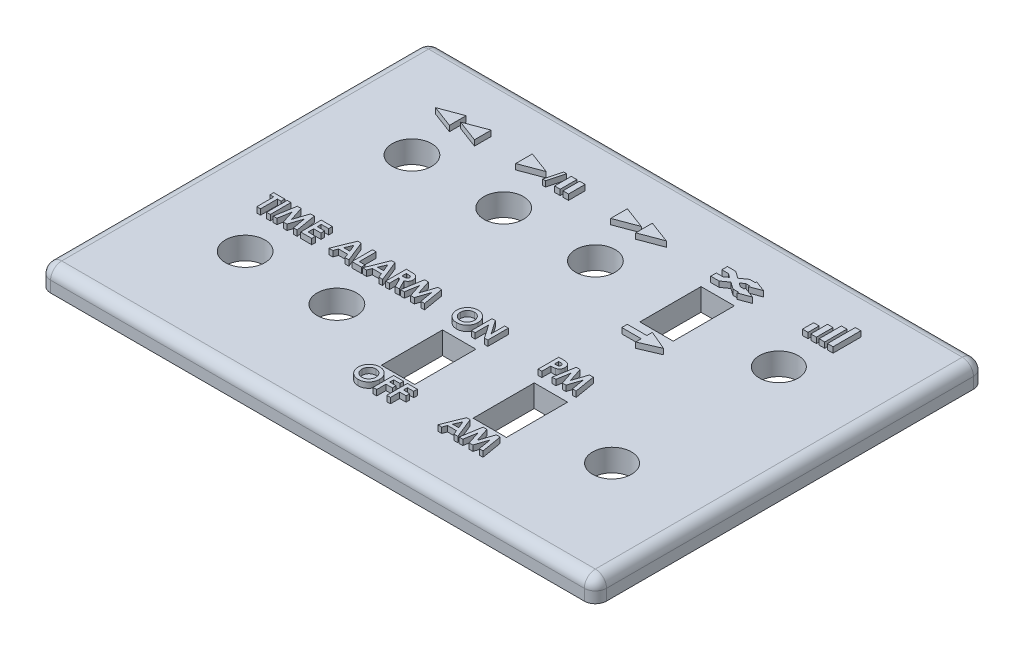
SolidWorks part; units mm, degrees
ref_plane "Front Plane" through (0, 0, 0) normal (0, 0, 1) x (1, 0, 0)
ref_plane "Top Plane" through (0, 0, 0) normal (0, 1, 0) x (1, 0, 0)
ref_plane "Right Plane" through (0, 0, 0) normal (1, 0, 0) x (0, 0, -1)
sketch "Sketch1" plane through (0, 0, 0) normal (0, 1, 0) x (1, 0, 0)
  line L0 (44.75, -15) -> (50, -15) construction
  line L1 (-50, -35) -> (50, -35)
  line L2 (-50, -35) -> (-50, 35)
  line L3 (-50, 35) -> (50, 35)
  line L4 (50, -35) -> (50, 35)
  line L5 (-50, -35) -> (50, 35) construction
  line L6 (-50, 35) -> (50, -35) construction
  circle A0 centre (33, -15) radius 11.75 construction
  point P0 (0, 0)
  dimension "D1" = 100
  dimension "D2" = 70
  dimension "D3" = 5.25
extrude "Boss-Extrude1" add sketch "Sketch1" along normal blind 4
sketch "Sketch2" plane through (0, 4, 0) normal (0, 1, 0) x (1, 0, 0)
  line L0 (-33, 15) -> (-16.5, 15) construction
  line L1 (13.5, 9.5) -> (19.5, 9.5)
  line L2 (13.5, 9.5) -> (13.5, 20.5)
  line L3 (13.5, 20.5) -> (19.5, 20.5)
  line L4 (19.5, 9.5) -> (19.5, 20.5)
  line L5 (13.5, 9.5) -> (19.5, 20.5) construction
  line L6 (13.5, 20.5) -> (19.5, 9.5) construction
  line L7 (-3, -9.5) -> (3, -9.5)
  line L8 (-3, -9.5) -> (-3, -20.5)
  line L9 (-3, -20.5) -> (3, -20.5)
  line L10 (3, -9.5) -> (3, -20.5)
  line L11 (-3, -9.5) -> (3, -20.5) construction
  line L12 (-3, -20.5) -> (3, -9.5) construction
  line L13 (13.5, -9.5) -> (19.5, -9.5)
  line L14 (13.5, -9.5) -> (13.5, -20.5)
  line L15 (13.5, -20.5) -> (19.5, -20.5)
  line L16 (19.5, -9.5) -> (19.5, -20.5)
  line L17 (13.5, -9.5) -> (19.5, -20.5) construction
  line L18 (13.5, -20.5) -> (19.5, -9.5) construction
  line L19 (-16.5, 15) -> (0, 15) construction
  line L20 (-33, -15) -> (-16.5, -15) construction
  line L21 (0, 15) -> (16.5, 15) construction
  line L22 (16.5, 15) -> (33, 15) construction
  line L23 (-16.5, -15) -> (0, -15) construction
  line L24 (0, -15) -> (16.5, -15) construction
  line L25 (16.5, -15) -> (33, -15) construction
  line L26 (-33, 15) -> (-50, 15) construction
  line L27 (-50, 35) -> (-50, -35) construction
  line L28 (33, 15) -> (50, 15) construction
  line L29 (50, -35) -> (50, 35) construction
  line L30 (-33, 15) -> (-33, 35) construction
  line L31 (50, 35) -> (-50, 35) construction
  line L32 (-33, -15) -> (-33, -35) construction
  line L33 (-50, -35) -> (50, -35) construction
  circle A0 centre (-33, -15) radius 3.55
  circle A1 centre (-16.5, -15) radius 3.55
  circle A2 centre (33, -15) radius 3.5
  circle A4 centre (-33, 15) radius 3.55
  circle A5 centre (-16.5, 15) radius 3.55
  circle A6 centre (0, 15) radius 3.55
  circle A7 centre (33, 15) radius 3.5
  point P4 (0, -15)
  point P14 (16.5, 15)
  point P21 (16.5, -15)
  dimension "D1" = 7
  dimension "D2" = 7.1
  dimension "D3" = 11
  dimension "D4" = 16.5
  dimension "D5" = 30
  dimension "D6" = 6
extrude "Cut-Extrude1" cut sketch "Sketch2" against normal through all
sketch "Sketch4" plane through (0, 4, 0) normal (0, 1, 0) x (1, 0, 0)
  line L0 (-33.25, 22) -> (-37.25, 23.5)
  line L1 (-37.25, 23.5) -> (-33.25, 25)
  line L2 (-33.25, 25) -> (-33.25, 22)
  line L3 (-37.25, 23.5) -> (-33.25, 23.5) construction
  line L4 (-28.75, 22) -> (-32.75, 23.5)
  line L5 (-32.75, 23.5) -> (-28.75, 25)
  line L6 (-28.75, 25) -> (-28.75, 22)
  line L7 (-32.75, 23.5) -> (-28.75, 23.5) construction
  line L8 (-33, 15) -> (-33, 38.4844) construction
  line L9 (-16.5, 15) -> (-16.5, 59.3156) construction
  line L10 (0, 15) -> (0, 58.3812) construction
  line L11 (-0.25, 23.5) -> (-4.25, 23.5) construction
  line L12 (4.25, 23.5) -> (0.25, 23.5) construction
  line L13 (-4.25, 25) -> (-4.25, 22)
  line L14 (-0.25, 23.5) -> (-4.25, 25)
  line L15 (-4.25, 22) -> (-0.25, 23.5)
  line L16 (0.25, 25) -> (0.25, 22)
  line L17 (4.25, 23.5) -> (0.25, 25)
  line L18 (0.25, 22) -> (4.25, 23.5)
  line L19 (-21.3393, 25) -> (-21.3393, 22)
  line L20 (-14.3393, 22) -> (-13.3393, 22)
  line L21 (-14.3393, 22) -> (-14.3393, 25)
  line L22 (-14.3393, 25) -> (-13.3393, 25)
  line L23 (-13.3393, 22) -> (-13.3393, 25)
  line L24 (-12.8393, 22) -> (-11.8393, 22)
  line L25 (-12.8393, 22) -> (-12.8393, 25)
  line L26 (-12.8393, 25) -> (-11.8393, 25)
  line L27 (-11.8393, 22) -> (-11.8393, 25)
  line L28 (-21.3393, 22) -> (-17.3393, 23.5)
  line L29 (-17.3393, 23.5) -> (-21.3393, 25)
  line L30 (-17.3393, 23.5) -> (-21.3393, 23.5) construction
  line L31 (-16.5, 22) -> (-15.6962, 25)
  line L32 (-15.6962, 25) -> (-15.1785, 25)
  line L33 (-15.1785, 25) -> (-15.9824, 22)
  line L34 (-15.9824, 22) -> (-16.5, 22)
  line L35 (-16.5, 22) -> (-15.1785, 25) construction
  line L36 (-11.2285, 22) -> (-11.8393, 22) construction
  line L37 (-15.6962, 25) -> (-15.9824, 22) construction
  line L38 (13.75, 25) -> (15.25, 25)
  line L39 (15.25, 25) -> (18.0687, 23)
  line L40 (18.0687, 23) -> (18.75, 23)
  line L41 (18.75, 23) -> (18.75, 23.25)
  line L42 (18.75, 23.25) -> (20.75, 22.5)
  line L43 (20.75, 22.5) -> (18.75, 21.75)
  line L44 (18.75, 21.75) -> (18.75, 22)
  line L45 (18.75, 22) -> (17.75, 22)
  line L46 (17.75, 22) -> (14.9313, 24)
  line L47 (14.9313, 24) -> (13.75, 24)
  line L48 (13.75, 23) -> (14.9313, 23)
  line L49 (14.9313, 23) -> (17.75, 25)
  line L50 (17.75, 25) -> (18.75, 25)
  line L51 (18.75, 25) -> (18.75, 25.25)
  line L52 (18.75, 25.25) -> (20.75, 24.5)
  line L53 (20.75, 24.5) -> (18.75, 23.75)
  line L54 (18.75, 23.75) -> (18.75, 24)
  line L55 (18.75, 24) -> (18.0687, 24)
  line L56 (18.0687, 24) -> (15.25, 22)
  line L57 (15.25, 22) -> (13.75, 22)
  line L58 (13.75, 22) -> (13.75, 23)
  line L59 (13.75, 24) -> (13.75, 25)
  line L60 (13.5, 9.5) -> (19.5, 9.5) construction
  line L61 (16.5, 9.5) -> (16.5, 48.0375) construction
  line L62 (13.75, 7) -> (17.25, 7)
  line L63 (17.25, 7) -> (17.25, 8)
  line L64 (17.25, 8) -> (20.75, 6.5)
  line L65 (20.75, 6.5) -> (17.25, 5)
  line L66 (17.25, 5) -> (17.25, 6)
  line L67 (17.25, 6) -> (13.75, 6)
  line L68 (13.75, 6) -> (13.75, 7)
  line L69 (26.3972, 23.5) -> (38.927, 23.5) construction
  line L70 (30.25, 22) -> (35.75, 22) construction
  line L71 (30.25, 22) -> (31.25, 22)
  line L72 (30.25, 22) -> (30.25, 24)
  line L73 (30.25, 24) -> (31.25, 24)
  line L74 (31.25, 22) -> (31.25, 24)
  line L75 (31.75, 22) -> (32.75, 22)
  line L76 (31.75, 22) -> (31.75, 25)
  line L77 (31.75, 25) -> (32.75, 25)
  line L78 (32.75, 22) -> (32.75, 25)
  line L79 (33.25, 22) -> (34.25, 22)
  line L80 (33.25, 22) -> (33.25, 26)
  line L81 (33.25, 26) -> (34.25, 26)
  line L82 (34.25, 22) -> (34.25, 26)
  line L83 (34.75, 22) -> (35.75, 22)
  line L84 (34.75, 22) -> (34.75, 27)
  line L85 (34.75, 27) -> (35.75, 27)
  line L86 (35.75, 22) -> (35.75, 27)
  line L87 (33, 22) -> (33, 15)
  line L92 (50, -35) -> (50, 35)
  line L93 (50, 35) -> (-50, 35)
  line L94 (-50, 35) -> (-50, -35)
  line L95 (-50, -35) -> (50, -35)
  line L96 (50, -35) -> (50, 35)
  line L97 (50, 35) -> (-50, 35)
  line L98 (-50, 35) -> (-50, -35)
  line L99 (-50, -35) -> (50, -35)
  circle A0 centre (33, 15) radius 3.5 construction
  circle A1 centre (33, 15) radius 3.5 construction
  point P35 (-15.8393, 23.5)
  point P70 (16.5, 22.8869)
  point P78 (17.364, 23.5)
  dimension "D1" = 4
  dimension "D2" = 3
  dimension "D3" = 0.5
  dimension "D4" = 0.25
  dimension "D5" = 8.5
  dimension "D6" = 3
  dimension "D7" = 4
  dimension "D8" = 0.5
  dimension "D9" = 3
  dimension "D10" = 7
  dimension "D11" = 3
  dimension "D12" = 1
  dimension "D13" = 0.5
  dimension "D14" = 1.5
  dimension "D15" = 1.5
  dimension "D16" = 75
  dimension "D17" = 1
  dimension "D18" = 1
  dimension "D19" = 1
  dimension "D20" = 1
  dimension "D21" = 1
  dimension "D22" = 1
  dimension "D23" = 1.5
  dimension "D24" = 3
  dimension "D25" = 7
  dimension "D26" = 1.5
  dimension "D27" = 2
  dimension "D28" = 3
  dimension "D29" = 8.5
  dimension "D30" = 1
  dimension "D31" = 3
  dimension "D32" = 7
  dimension "D33" = 3.5
  dimension "D34" = 8.5
  dimension "D35" = 0.5
  dimension "D36" = 1
  dimension "D37" = 0.5
  dimension "D38" = 0.5
  dimension "D39" = 1
  dimension "D40" = 1
  dimension "D41" = 1
  dimension "D43" = 5
  dimension "D42" = 0
extrude "Boss-Extrude5" add sketch "Sketch4" along normal blind 1 contours L2 L1 L0 | L6 L5 L4 | L28 L29 L19 | L34 L33 L32 L31 | L20 L23 L22 L21 | L24 L27 L26 L25 | L13 L15 L14 | L16 L18 L17 | L59 L47 L46 L49 L39 L38 | L56 L55 L54 L53 L52 L51 L50 L49 L39 | L56 L39 L49 L46 | L58 L57 L56 L46 L49 L48 | L39 L56 L46 L45 L44 L43 L42 L41 L40 | L68 L67 L66 L65 L64 L63 L62 | L71 L74 L73 L72 | L75 L78 L77 L76 | L79 L82 L81 L80 | L83 L86 L85 L84
sketch "Sketch5" plane through (0, 4, 0) normal (0, 1, 0) x (1, 0, 0)
  line L0 (-38.6119, -8) -> (-27.3881, -8) construction
  line L1 (-25.0167, -8) -> (-7.9833, -8) construction
  line L2 (-4.0464, -8) -> (4.0464, -8) construction
  line L3 (-33, -8) -> (-33, -15) construction
  line L4 (12.2763, -8) -> (20.7237, -8) construction
  line L5 (-16.5, -8) -> (-16.5, -15) construction
  line L6 (0, -8) -> (0, -15) construction
  line L7 (16.5, -8) -> (16.5, -15) construction
  line L8 (0, -15) -> (0, -25.7) construction
  line L9 (16.5, -15) -> (16.5, -25.7) construction
  line L10 (-4.0464, -25.7) -> (4.0464, -25.7) construction
  line L11 (12.2763, -25.7) -> (20.7237, -25.7) construction
  line L12 (-33, -15) -> (33, -15) construction
  line L13 (-3, -9.5) -> (3, -20.5) construction
  line L14 (-3, -20.5) -> (3, -9.5) construction
  line L15 (13.5, -9.5) -> (19.5, -20.5) construction
  line L16 (13.5, -20.5) -> (19.5, -9.5) construction
  circle A0 centre (-33, -15) radius 3.55 construction
  circle A1 centre (-33, -15) radius 3.55 construction
  text T0 "<b>TIME</b>" font "Century Gothic" height in points 14
  text T1 "<b>ALARM</b>" font "Century Gothic" height in points 14
  text T2 "<b>ON</b>" font "Century Gothic" height in points 14
  text T3 "<b>OFF</b>" font "Century Gothic" height in points 14
  text T4 "<b>PM</b>" font "Century Gothic" height in points 14
  text T5 "<b>AM</b>" font "Century Gothic" height in points 14
  dimension "D1" = 7
  dimension "D2" = 10.7
  dimension "D3" = 10.7
extrude "Boss-Extrude6" add sketch "Sketch5" along normal blind 1
fillet "Fillet1" radius 2 8 edges at (0, 4, 35) (-50, 4, 0) (0, 4, -35) (50, 4, 0) (50, 2, 35) (-50, 2, 35) (-50, 2, -35) (50, 2, -35)
